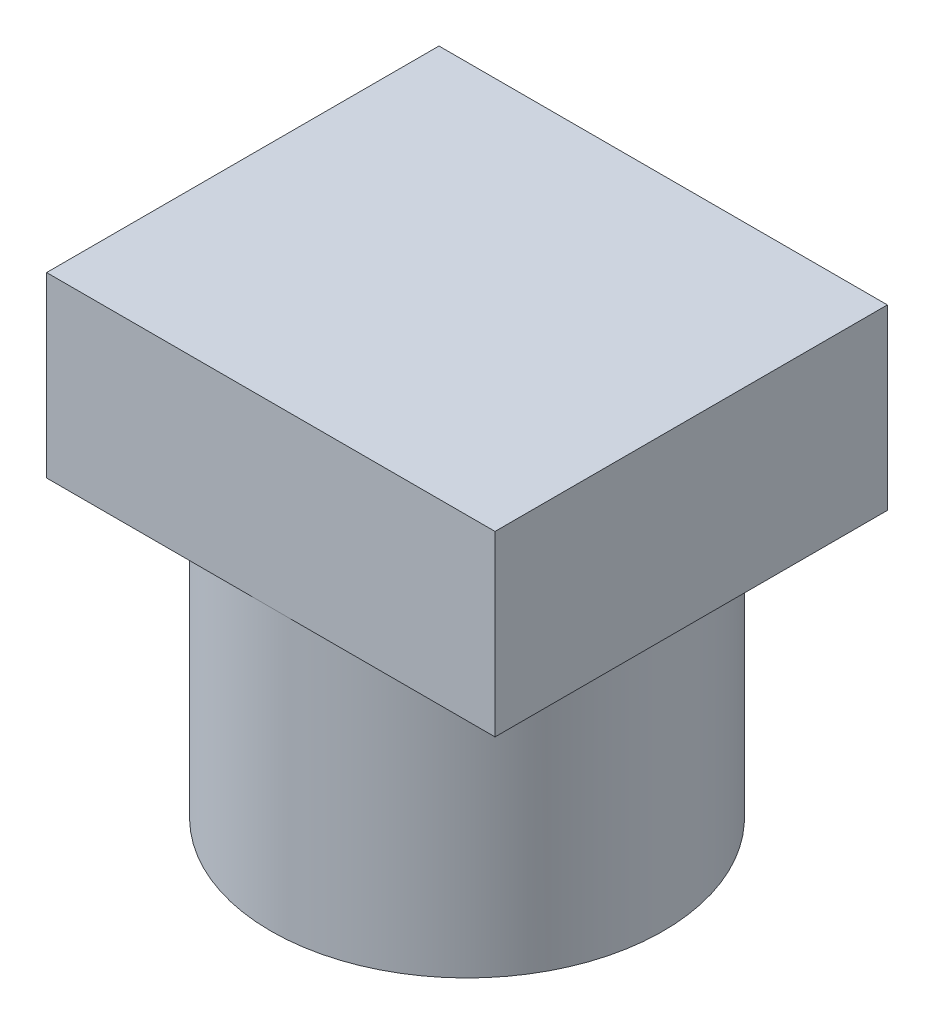
SolidWorks part; units mm, degrees
ref_plane "Front Plane" through (0, 0, 0) normal (0, 0, 1) x (1, 0, 0)
ref_plane "Top Plane" through (0, 0, 0) normal (0, 1, 0) x (1, 0, 0)
ref_plane "Right Plane" through (0, 0, 0) normal (1, 0, 0) x (0, 0, -1)
sketch "Sketch1" plane through (0, 0, 0) normal (0, 1, 0) x (1, 0, 0)
  circle A0 centre (0, 0) radius 2
  circle A1 centre (0, 0) radius 3.5
  dimension "D1" = 4
  dimension "D2" = 7
extrude "Boss-Extrude1" add sketch "Sketch1" along normal blind 5
sketch "Sketch2" plane through (0, 5, 0) normal (0, 1, 0) x (1, 0, 0)
  line L1 (-4, 3.5) -> (4, 3.5)
  line L2 (-4, 3.5) -> (-4, -3.5)
  line L3 (-4, -3.5) -> (4, -3.5)
  line L4 (4, 3.5) -> (4, -3.5)
  point P4 (0, 3.5)
  point P5 (-4, 0)
  dimension "D1" = 7
  dimension "D2" = 8
extrude "Boss-Extrude2" add sketch "Sketch2" along normal blind 3.175
